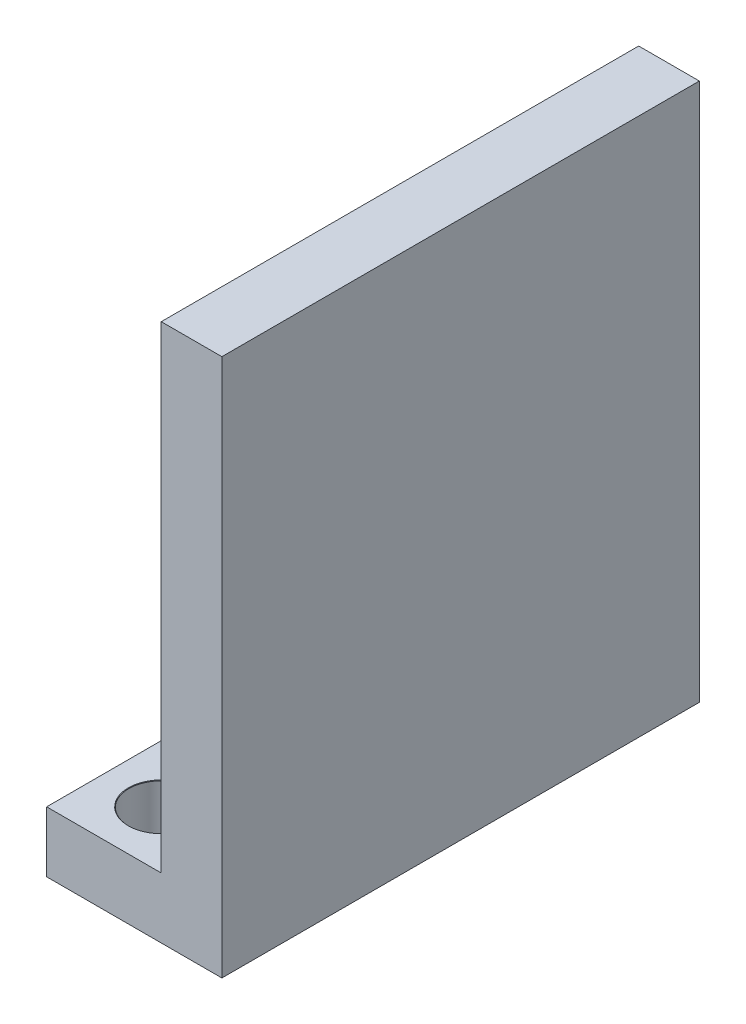
SolidWorks part; units mm, degrees
ref_plane "Front Plane" through (0, 0, 0) normal (0, 0, 1) x (1, 0, 0)
ref_plane "Top Plane" through (0, 0, 0) normal (0, 1, 0) x (1, 0, 0)
ref_plane "Right Plane" through (0, 0, 0) normal (1, 0, 0) x (0, 0, -1)
sketch "Sketch1" plane through (0, 0, 0) normal (0, 1, 0) x (1, 0, 0)
  line L1 (0, 0) -> (9.175, 0)
  line L2 (0, 0) -> (0, 25)
  line L3 (0, 25) -> (9.175, 25)
  line L4 (9.175, 0) -> (9.175, 25)
  dimension "D1" = 25
  dimension "D2" = 9.175
extrude "Boss-Extrude1" add sketch "Sketch1" along normal blind 3.175
sketch "Sketch2" plane through (0, 3.175, 0) normal (0, 1, 0) x (1, 0, 0)
  line L1 (9.175, 0) -> (6, 0)
  line L2 (9.175, 0) -> (9.175, 25)
  line L3 (9.175, 25) -> (6, 25)
  line L4 (6, 0) -> (6, 25)
  dimension "D1" = 3.175
extrude "Boss-Extrude2" add sketch "Sketch2" along normal blind 25
hole_wizard "M3 Clearance Hole1" positions "Sketch3" profile "Sketch4" hole size "M3" standard "ANSI Metric" end condition through all
sketch "Sketch3" plane through (0, 3.175, 0) normal (0, 1, 0) x (1, 0, 0)
  line L0 (6, 25) -> (6, 0) construction
  line L1 (6, 25) -> (0, 25) construction
  line L2 (6, 25) -> (6, 0) construction
  point P0 (3, 22)
  point P2 (3, 3)
  dimension "D1" = 3
  dimension "D2" = 19
  dimension "D3" = 3
  dimension "D4" = 3
sketch "Sketch4" plane through (3, 3.175, -22) normal (1, 0, 0) x (0, 0, 1)
  line L0 (0, 0) -> (0, 3.175)
  line L1 (0, 3.175) -> (1.7, 3.175)
  line L2 (1.7, 3.175) -> (1.7, 0.025)
  line L3 (1.7, 0.025) -> (1.725, 0)
  line L5 (1.725, 0) -> (0, 0)
  line L6 (-1.7, 0.025) -> (-1.725, 0) construction
  line L11 (0, -6.35) -> (0, 107.95) construction
  dimension "Thru Hole Dia." = 3.4
  dimension "Thru Hole Depth" = 3.175
  dimension "Near C'Sink Dia." = 3.45
  dimension "Near C'Sink Angle" = 90
